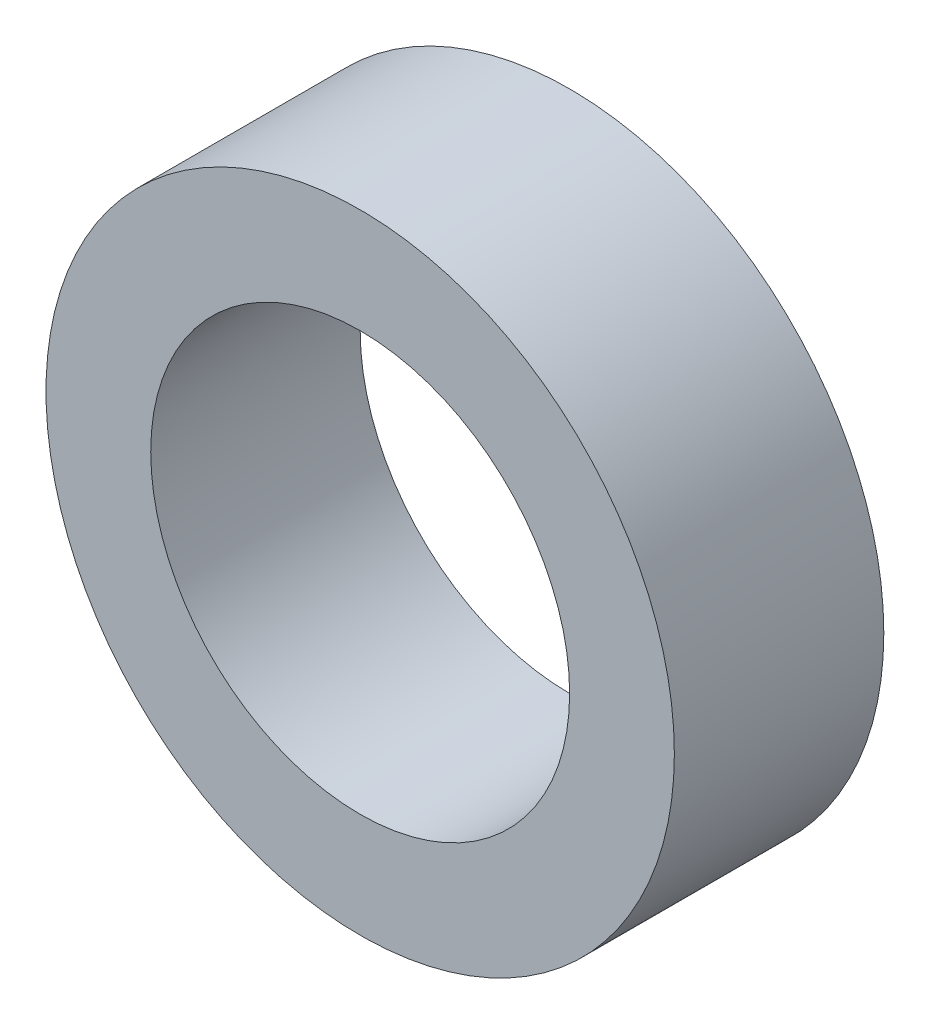
SolidWorks part; units mm, degrees
ref_plane "Front Plane" through (0, 0, 0) normal (0, 0, 1) x (1, 0, 0)
ref_plane "Top Plane" through (0, 0, 0) normal (0, 1, 0) x (1, 0, 0)
ref_plane "Right Plane" through (0, 0, 0) normal (1, 0, 0) x (0, 0, -1)
sketch "Sketch1" plane through (0, 0, 0) normal (0, 0, 1) x (1, 0, 0)
  circle A0 centre (0, 0) radius 15
  circle A1 centre (0, 0) radius 10
  dimension "D1" = 30
  dimension "D2" = 20
extrude "Boss-Extrude1" add sketch "Sketch1" along normal blind 10
